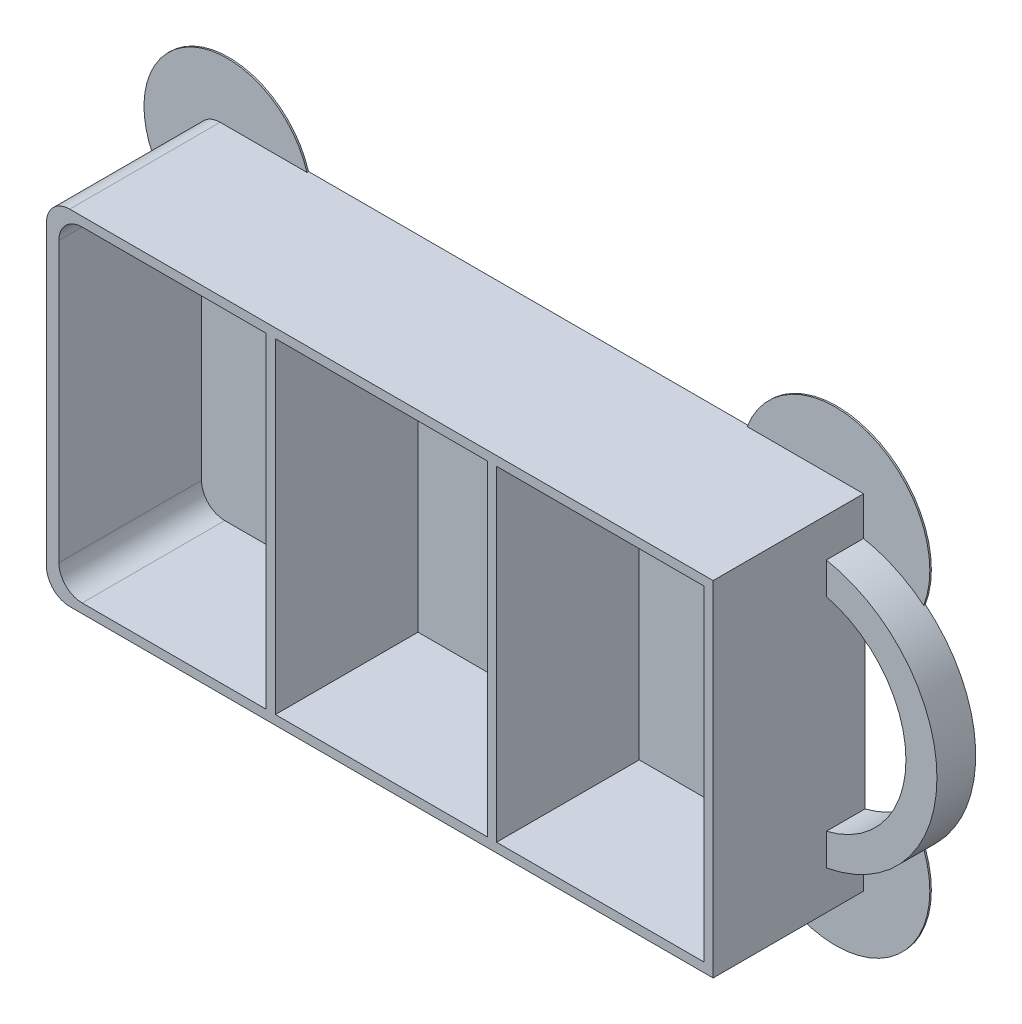
SolidWorks part; units mm, degrees
ref_plane "Спереди" through (0, 0, 0) normal (0, 0, 1) x (1, 0, 0)
ref_plane "Сверху" through (0, 0, 0) normal (0, 1, 0) x (1, 0, 0)
ref_plane "Справа" through (0, 0, 0) normal (1, 0, 0) x (0, 0, -1)
other "Configuration Table"
sketch "Эскиз1" plane through (0, 0, 0) normal (0, 0, 1) x (1, 0, 0)
  line L1 (-43, 22.2) -> (43, 22.2)
  line L2 (-43, 22.2) -> (-43, -22.2)
  line L3 (-43, -22.2) -> (43, -22.2)
  line L4 (43, 22.2) -> (43, -22.2)
  line L5 (-43, 22.2) -> (43, -22.2) construction
  line L6 (-43, -22.2) -> (43, 22.2) construction
  point P0 (0, 0)
  dimension "D1" = 86
  dimension "D2" = 44.4
extrude "Бобышка-Вытянуть1" add sketch "Эскиз1" along normal blind 19.6
sketch "Эскиз2" plane through (0, 0, 0) normal (0, 0, 1) x (1, 0, 0)
  line L0 (0, 0) -> (43, 0) construction
  line L1 (43, -22.2) -> (43, 22.2) construction
  line L2 (43, 17.2) -> (43, 13.1088)
  line L3 (43, -17.2) -> (43, -13.1088)
  arc A0 (43, -17.2) -> (43, 17.2) centre (39.7735, 0) ccw
  arc A1 (43, -13.1088) -> (43, 13.1088) centre (39.7735, 0) ccw
  dimension "D3" = 13.5
  dimension "D4" = 4
  dimension "D1" = 5
  dimension "D2" = 5
extrude "Бобышка-Вытянуть2" add sketch "Эскиз2" along normal blind 5
sketch "Эскиз3" plane through (0, 0, 19.6) normal (0, 0, 1) x (1, 0, 0)
  line L0 (41.8, 0) -> (-41.4, 0) construction
  line L2 (-14.6667, -21) -> (-13.4667, -21)
  line L3 (-14.6667, -21) -> (-14.6667, 21)
  line L4 (-14.6667, 21) -> (-13.4667, 21)
  line L5 (-41.4, 22.2) -> (-41.4, -22.2)
  line L6 (-43, -21) -> (41.8, -21)
  line L7 (41.8, -21) -> (41.8, 21)
  line L8 (41.8, 21) -> (-43, 21)
  line L9 (-41.4, -21) -> (41.8, -21)
  line L10 (41.8, -21) -> (41.8, 21)
  line L11 (41.8, 21) -> (-41.4, 21)
  line L12 (-41.4, 21) -> (-41.4, -21)
  line L13 (-13.4667, -21) -> (-13.4667, 21)
  line L14 (-14.6667, -21) -> (-13.4667, 21) construction
  line L15 (-14.6667, 21) -> (-13.4667, -21) construction
  line L16 (13.8667, 21) -> (15.0667, 21)
  line L17 (13.8667, 21) -> (13.8667, -21)
  line L18 (13.8667, -21) -> (15.0667, -21)
  line L19 (15.0667, 21) -> (15.0667, -21)
  line L20 (13.8667, 21) -> (15.0667, -21) construction
  line L21 (13.8667, -21) -> (15.0667, 21) construction
  point P9 (-14.0667, 0)
  point P15 (14.4667, 0)
  dimension "D3" = 1.2
  dimension "D4" = 1.2
  dimension "D5" = 83.2
  dimension "D6" = 27.3333
  dimension "D7" = 27.3333
  dimension "D8" = 27.3333
  dimension "D1" = 1.2
  dimension "D2" = 1.6
extrude "Вырез-Вытянуть1" cut sketch "Эскиз3" against normal offset from surface (18.4 mm away) 1.2 contours L11 L12 L9 L3 | L17 L11 L13 L9 | L11 L19 L9 L10 up to face at (48.1368, 0, 0)
fillet "Скругление1" radius 3 4 edges at (-43, 22.2, 9.8) (-43, -22.2, 9.8) (-41.4, -21, 10.4) (-41.4, 21, 10.4)
sketch "Эскиз4" plane through (0, 0, 0) normal (0, 0, -1) x (-1, 0, 0)
  line L0 (-43, 22.2) -> (40, 22.2) construction
  line L1 (0, 0) -> (-22.3839, 0) construction
  line L2 (0, 0) -> (0, 10.6067) construction
  line L3 (-50.772, 13.6119) -> (-27.9898, 22.2)
  line L4 (-50.772, -13.6119) -> (-27.9898, -22.2)
  line L5 (43, 19.2) -> (43, -19.2) construction
  line L6 (43, 9.0687) -> (28.7935, 22.2)
  line L7 (43, -9.0687) -> (28.7935, -22.2)
  arc A0 (-27.9898, 22.2) -> (-50.772, 13.6119) centre (-39.3809, 17.9059) ccw
  arc A1 (-43, 17.2) -> (-43, -17.2) centre (-39.7735, 0) ccw construction
  arc A2 (-27.9898, -22.2) -> (-50.772, -13.6119) centre (-39.3809, -17.9059) cw
  arc A3 (28.7935, 22.2) -> (43, 9.0687) centre (39.0748, 19.0727) cw
  arc A4 (28.7935, -22.2) -> (43, -9.0687) centre (39.0748, -19.0727) ccw
extrude "Бобышка-Вытянуть3" add sketch "Эскиз4" against normal blind 0.2
equation "\"D4@Эскиз3\"=\"D3@Эскиз3\""
equation "\"D6@Эскиз3\"=(\"D5@Эскиз3\"/3)-0.4"
equation "\"D7@Эскиз3\"=(\"D5@Эскиз3\"/3)-0.4"
